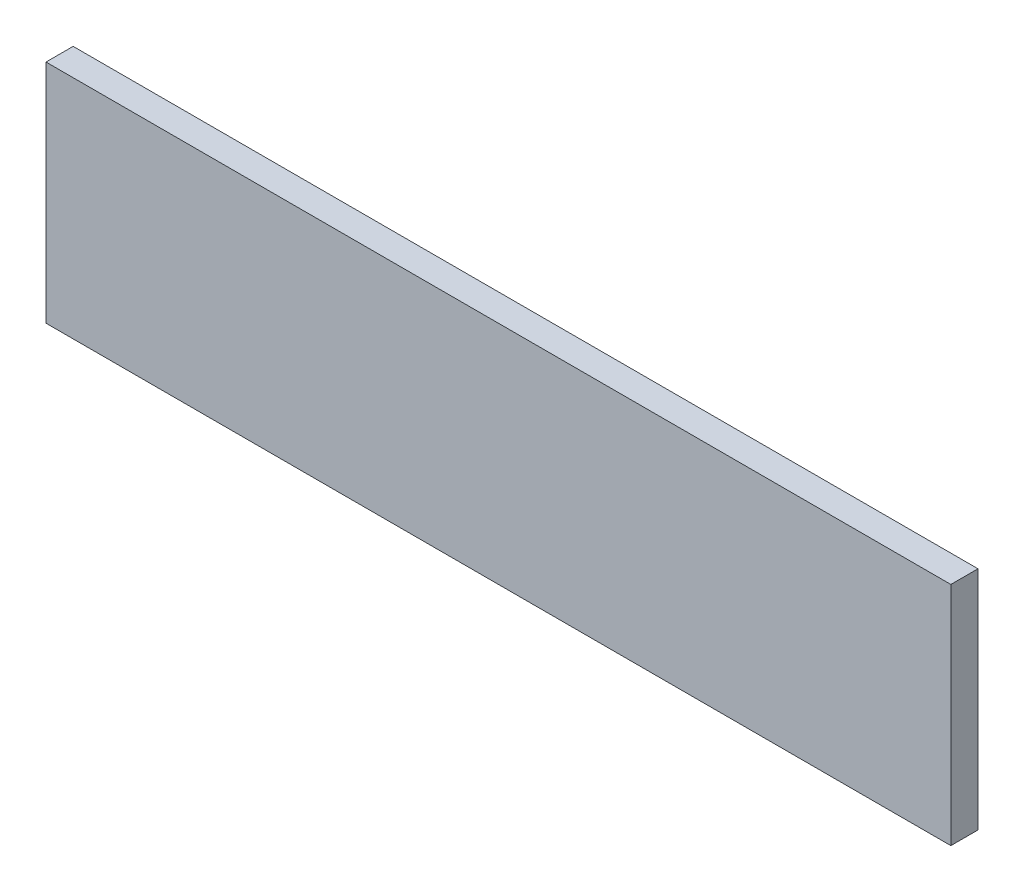
SolidWorks part; units mm, degrees
ref_plane "Front Plane" through (0, 0, 0) normal (0, 0, 1) x (1, 0, 0)
ref_plane "Top Plane" through (0, 0, 0) normal (0, 1, 0) x (1, 0, 0)
ref_plane "Right Plane" through (0, 0, 0) normal (1, 0, 0) x (0, 0, -1)
sketch "Sketch1" plane through (0, 0, 0) normal (0, 0, 1) x (1, 0, 0)
  line L1 (-63.3588, 52.799) -> (36.6412, 52.799)
  line L2 (-63.3588, 52.799) -> (-63.3588, 27.799)
  line L3 (-63.3588, 27.799) -> (36.6412, 27.799)
  line L4 (36.6412, 52.799) -> (36.6412, 27.799)
  dimension "D1" = 100
  dimension "D2" = 25
extrude "Boss-Extrude1" add sketch "Sketch1" along normal blind 3
